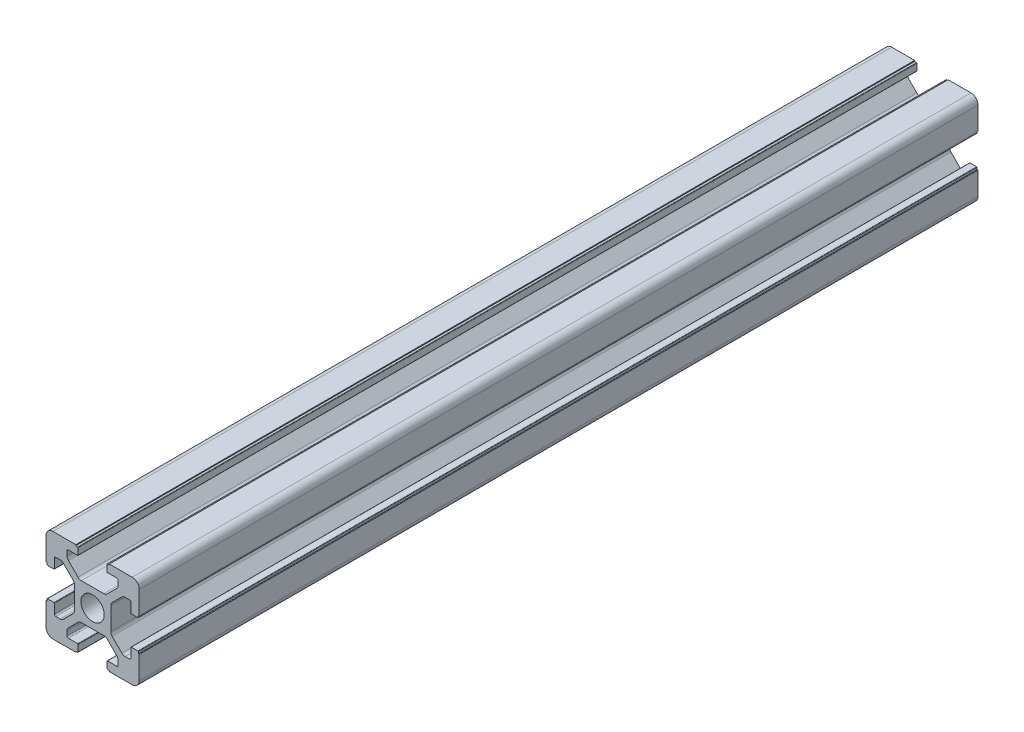
SolidWorks part; units mm, degrees
material "6063-T5"
ref_plane "前视基准面" through (0, 0, 0) normal (0, 0, 1) x (1, 0, 0)
ref_plane "上视基准面" through (0, 0, 0) normal (0, 1, 0) x (1, 0, 0)
ref_plane "右视基准面" through (0, 0, 0) normal (1, 0, 0) x (0, 0, -1)
sketch "草图1" plane through (0, 0, 0) normal (0, 0, 1) x (1, 0, 0)
  line L0 (-1.4389, 10) -> (24.3741, 10) construction
  line L1 (20, 13.6) -> (20, 20)
  line L2 (0, 0) -> (0, 6.4)
  line L3 (0, 20) -> (6.4, 20)
  line L4 (20, 0) -> (20, 6.4)
  line L5 (10, 21.5388) -> (10, -2.4017) construction
  line L6 (6.9, 18.3) -> (6.9, 19.7)
  line L7 (6.8, 18.2) -> (4.8, 18.2)
  line L8 (4.5, 17.9) -> (4.5, 16.9749)
  line L9 (4.7929, 16.2678) -> (6.8678, 14.1929)
  line L10 (7.5749, 13.9) -> (12.4251, 13.9)
  line L11 (6.8, 19.8) -> (6.4, 19.8)
  line L12 (6.4, 19.8) -> (6.4, 20)
  line L13 (0, 13.6) -> (0.2, 13.6)
  line L14 (0.2, 13.6) -> (0.2, 13.2)
  line L15 (0.3, 13.1) -> (1.7, 13.1)
  line L16 (1.8, 13.2) -> (1.8, 15.2)
  line L17 (2.1, 15.5) -> (3.0251, 15.5)
  line L18 (3.7322, 15.2071) -> (5.8071, 13.1322)
  line L19 (6.1, 12.4251) -> (6.1, 7.5749)
  line L20 (13.6, 19.8) -> (13.6, 20)
  line L21 (13.2, 19.8) -> (13.6, 19.8)
  line L22 (13.1, 18.3) -> (13.1, 19.7)
  line L23 (13.2, 18.2) -> (15.2, 18.2)
  line L24 (15.5, 17.9) -> (15.5, 16.9749)
  line L25 (15.2071, 16.2678) -> (13.1322, 14.1929)
  line L26 (0, 6.4) -> (0.2, 6.4)
  line L27 (0.2, 6.4) -> (0.2, 6.8)
  line L28 (0.3, 6.9) -> (1.7, 6.9)
  line L29 (1.8, 6.8) -> (1.8, 4.8)
  line L30 (2.1, 4.5) -> (3.0251, 4.5)
  line L31 (3.7322, 4.7929) -> (5.8071, 6.8678)
  line L32 (13.6, 20) -> (20, 20)
  line L33 (0, 13.6) -> (0, 20)
  line L34 (13.6, 0.2) -> (13.6, 0)
  line L35 (13.2, 0.2) -> (13.6, 0.2)
  line L36 (13.1, 1.7) -> (13.1, 0.3)
  line L37 (13.2, 1.8) -> (15.2, 1.8)
  line L38 (15.5, 2.1) -> (15.5, 3.0251)
  line L39 (15.2071, 3.7322) -> (13.1322, 5.8071)
  line L40 (4.5, 2.1) -> (4.5, 3.0251)
  line L41 (6.8, 1.8) -> (4.8, 1.8)
  line L42 (6.4, 0.2) -> (6.4, 0)
  line L43 (6.8, 0.2) -> (6.4, 0.2)
  line L44 (6.9, 1.7) -> (6.9, 0.3)
  line L45 (4.7929, 3.7322) -> (6.8678, 5.8071)
  line L46 (7.5749, 6.1) -> (12.4251, 6.1)
  line L47 (20, 6.4) -> (19.8, 6.4)
  line L48 (19.8, 6.4) -> (19.8, 6.8)
  line L49 (19.7, 6.9) -> (18.3, 6.9)
  line L50 (18.2, 6.8) -> (18.2, 4.8)
  line L51 (17.9, 4.5) -> (16.9749, 4.5)
  line L52 (16.2678, 4.7929) -> (14.1929, 6.8678)
  line L53 (13.9, 12.4251) -> (13.9, 7.5749)
  line L54 (16.2678, 15.2071) -> (14.1929, 13.1322)
  line L55 (17.9, 15.5) -> (16.9749, 15.5)
  line L56 (18.2, 13.2) -> (18.2, 15.2)
  line L57 (19.7, 13.1) -> (18.3, 13.1)
  line L58 (19.8, 13.6) -> (19.8, 13.2)
  line L59 (20, 13.6) -> (19.8, 13.6)
  line L60 (0, 0) -> (6.4, 0)
  line L61 (13.6, 0) -> (20, 0)
  arc A0 (6.1, 12.4251) -> (5.8071, 13.1322) centre (5.1, 12.4251) ccw
  arc A1 (7.5749, 13.9) -> (6.8678, 14.1929) centre (7.5749, 14.9) cw
  arc A2 (4.5, 16.9749) -> (4.7929, 16.2678) centre (5.5, 16.9749) ccw
  arc A3 (3.7322, 15.2071) -> (3.0251, 15.5) centre (3.0251, 14.5) ccw
  arc A4 (4.5, 17.9) -> (4.8, 18.2) centre (4.8, 17.9) cw
  arc A5 (1.8, 15.2) -> (2.1, 15.5) centre (2.1, 15.2) cw
  arc A6 (0.3, 13.1) -> (0.2, 13.2) centre (0.3, 13.2) cw
  arc A7 (6.9, 19.7) -> (6.8, 19.8) centre (6.8, 19.7) ccw
  arc A8 (1.7, 13.1) -> (1.8, 13.2) centre (1.7, 13.2) ccw
  arc A9 (6.9, 18.3) -> (6.8, 18.2) centre (6.8, 18.3) cw
  arc A10 (13.1, 19.7) -> (13.2, 19.8) centre (13.2, 19.7) cw
  arc A11 (13.1, 18.3) -> (13.2, 18.2) centre (13.2, 18.3) ccw
  arc A12 (15.5, 17.9) -> (15.2, 18.2) centre (15.2, 17.9) ccw
  arc A13 (15.5, 16.9749) -> (15.2071, 16.2678) centre (14.5, 16.9749) cw
  arc A14 (12.4251, 13.9) -> (13.1322, 14.1929) centre (12.4251, 14.9) ccw
  arc A15 (0.3, 6.9) -> (0.2, 6.8) centre (0.3, 6.8) ccw
  arc A16 (1.7, 6.9) -> (1.8, 6.8) centre (1.7, 6.8) cw
  arc A17 (1.8, 4.8) -> (2.1, 4.5) centre (2.1, 4.8) ccw
  arc A18 (3.7322, 4.7929) -> (3.0251, 4.5) centre (3.0251, 5.5) cw
  arc A19 (6.1, 7.5749) -> (5.8071, 6.8678) centre (5.1, 7.5749) cw
  arc A20 (13.1, 0.3) -> (13.2, 0.2) centre (13.2, 0.3) ccw
  arc A21 (13.1, 1.7) -> (13.2, 1.8) centre (13.2, 1.7) cw
  arc A22 (15.5, 2.1) -> (15.2, 1.8) centre (15.2, 2.1) cw
  arc A23 (15.5, 3.0251) -> (15.2071, 3.7322) centre (14.5, 3.0251) ccw
  arc A24 (12.4251, 6.1) -> (13.1322, 5.8071) centre (12.4251, 5.1) cw
  arc A25 (4.5, 2.1) -> (4.8, 1.8) centre (4.8, 2.1) ccw
  arc A26 (6.9, 0.3) -> (6.8, 0.2) centre (6.8, 0.3) cw
  arc A27 (6.9, 1.7) -> (6.8, 1.8) centre (6.8, 1.7) ccw
  arc A28 (4.5, 3.0251) -> (4.7929, 3.7322) centre (5.5, 3.0251) cw
  arc A29 (7.5749, 6.1) -> (6.8678, 5.8071) centre (7.5749, 5.1) ccw
  arc A30 (19.7, 6.9) -> (19.8, 6.8) centre (19.7, 6.8) cw
  arc A31 (18.3, 6.9) -> (18.2, 6.8) centre (18.3, 6.8) ccw
  arc A32 (18.2, 4.8) -> (17.9, 4.5) centre (17.9, 4.8) cw
  arc A33 (16.2678, 4.7929) -> (16.9749, 4.5) centre (16.9749, 5.5) ccw
  arc A34 (13.9, 7.5749) -> (14.1929, 6.8678) centre (14.9, 7.5749) ccw
  arc A35 (13.9, 12.4251) -> (14.1929, 13.1322) centre (14.9, 12.4251) cw
  arc A36 (16.2678, 15.2071) -> (16.9749, 15.5) centre (16.9749, 14.5) cw
  arc A37 (18.2, 15.2) -> (17.9, 15.5) centre (17.9, 15.2) ccw
  arc A38 (18.3, 13.1) -> (18.2, 13.2) centre (18.3, 13.2) cw
  arc A39 (19.7, 13.1) -> (19.8, 13.2) centre (19.7, 13.2) ccw
  circle A40 centre (10, 10) radius 2.5
  point P39 (0.2, 13.1)
  point P42 (6.9, 19.8)
  point P45 (1.8, 13.1)
  point P48 (6.9, 18.2)
  point P66 (10, 13.9)
  point P83 (6.1, 10)
  dimension "D19" = 1
  dimension "D20" = 1
  dimension "D21" = 0.3
  dimension "D22" = 0.1
  dimension "D23" = 5
  dimension "D1" = 20
  dimension "D2" = 20
  dimension "D3" = 10
  dimension "D4" = 10
  dimension "D5" = 1.8
  dimension "D6" = 0.5
  dimension "D7" = 1.6
  dimension "D8" = 3.1
  dimension "D9" = 6.1
  dimension "D10" = 5.5
  dimension "D11" = 3.1
  dimension "D12" = 6.1
  dimension "D13" = 5.5
  dimension "D14" = 1.8
  dimension "D15" = 0.5
  dimension "D16" = 1.5
  dimension "D17" = 45
  dimension "D18" = 1.6
extrude "凸台-拉伸1" add sketch "草图1" along normal blind 180
fillet "圆角1" radius 1.5 4 edges at (20, 0, 90) (0, 0, 90) (0, 20, 90) (20, 20, 90)
